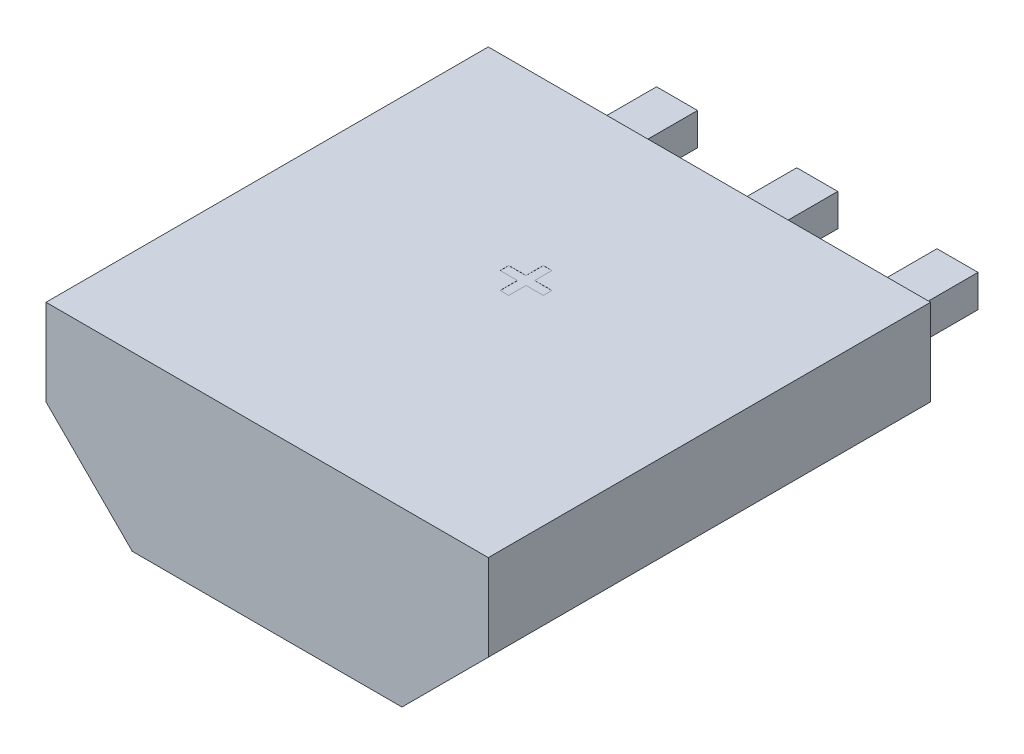
SolidWorks part; units mm, degrees
ref_plane "Plan de face" through (0, 0, 0) normal (0, 0, 1) x (1, 0, 0)
ref_plane "Plan de dessus" through (0, 0, 0) normal (0, 1, 0) x (1, 0, 0)
ref_plane "Plan de droite" through (0, 0, 0) normal (1, 0, 0) x (0, 0, -1)
ref_plane "Plan1" through (0, 0, 4.1) normal (0, 0, 1) x (1, 0, 0)
sketch "Esquisse1" plane through (0, 0, 4.1) normal (0, 0, 1) x (1, 0, 0)
  line L0 (-2.05, -0.8) -> (-1.25, -1.6)
  line L1 (-1.25, -1.6) -> (1.25, -1.6)
  line L2 (1.25, -1.6) -> (2.05, -0.8)
  line L3 (2.05, -0.8) -> (2.05, 0)
  line L4 (2.05, 0) -> (-2.05, 0)
  line L5 (-2.05, 0) -> (-2.05, -0.8)
extrude "Boitier" add sketch "Esquisse1" against normal blind 4.1
sketch "Esquisse2" plane through (0, 0, 0) normal (0, 0, -1) x (-1, 0, 0)
  line L0 (-0.19, -0.54) -> (0.19, -0.54)
  line L1 (0.19, -0.54) -> (0.19, -0.84)
  line L2 (0.19, -0.84) -> (-0.19, -0.84)
  line L3 (-0.19, -0.84) -> (-0.19, -0.54)
extrude "Pin2" add sketch "Esquisse2" along normal blind 1
sketch "Esquisse3" plane through (0, 0, 0) normal (0, 0, -1) x (-1, 0, 0)
  line L0 (-1.49, -0.54) -> (-1.11, -0.54)
  line L1 (-1.11, -0.54) -> (-1.11, -0.84)
  line L2 (-1.11, -0.84) -> (-1.49, -0.84)
  line L3 (-1.49, -0.84) -> (-1.49, -0.54)
extrude "Pin3" add sketch "Esquisse3" along normal blind 1
sketch "Esquisse4" plane through (0, 0, 0) normal (0, 0, -1) x (-1, 0, 0)
  line L0 (1.11, -0.54) -> (1.49, -0.54)
  line L1 (1.49, -0.54) -> (1.49, -0.84)
  line L2 (1.49, -0.84) -> (1.11, -0.84)
  line L3 (1.11, -0.84) -> (1.11, -0.54)
extrude "Pin1" add sketch "Esquisse4" along normal blind 1
ref_plane "Plan2" through (0, 0, 2.05) normal (0, 0, 1) x (1, 0, 0)
sketch "Esquisse5" plane through (0, -1.6, 0) normal (0, -1, 0) x (1, 0, 0)
  line L0 (-1.25, 0) -> (1.25, 0) construction
  circle A0 centre (0, 1.7) radius 0.2
  dimension "D2" = 0.4
  dimension "D1" = 1.7
extrude "Enlèv. mat.-Extru.1" cut sketch "Esquisse5" against normal blind 0.001
sketch "Esquisse6" plane through (0, 0, 0) normal (0, 1, 0) x (1, 0, 0)
  line L0 (0, 0) -> (0, -3.4) construction
  line L1 (0, -1.7) -> (-1.167, -1.7) construction
  line L2 (2.05, 0) -> (-2.05, 0) construction
  line L3 (0, -1.66) -> (-0.2, -1.66) construction
  line L4 (-0.2, -1.66) -> (-0.04, -1.66)
  line L5 (-0.2, -1.74) -> (-0.04, -1.74)
  line L6 (-0.2, -1.66) -> (-0.2, -1.74)
  line L7 (0.2, -1.66) -> (0.2, -1.74)
  line L8 (0.2, -1.74) -> (0.04, -1.74)
  line L9 (0.2, -1.66) -> (0.04, -1.66)
  line L10 (-0.04, -1.66) -> (-0.04, -1.5) construction
  line L11 (-0.04, -1.5) -> (0.04, -1.5) construction
  line L14 (-0.04, -1.9) -> (0.04, -1.9) construction
  line L15 (-0.04, -1.5) -> (0.04, -1.5)
  line L16 (-0.04, -1.5) -> (-0.04, -1.66)
  line L17 (-0.04, -1.74) -> (-0.04, -1.9) construction
  line L18 (0.04, -1.5) -> (0.04, -1.66)
  line L19 (0.04, -1.9) -> (0.04, -1.74)
  line L20 (-0.04, -1.9) -> (-0.04, -1.74)
  line L21 (-0.04, -1.9) -> (0.04, -1.9)
  dimension "D1" = 1.7
extrude "Enlèv. mat.-Extru.4" cut sketch "Esquisse6" against normal blind 0.001
